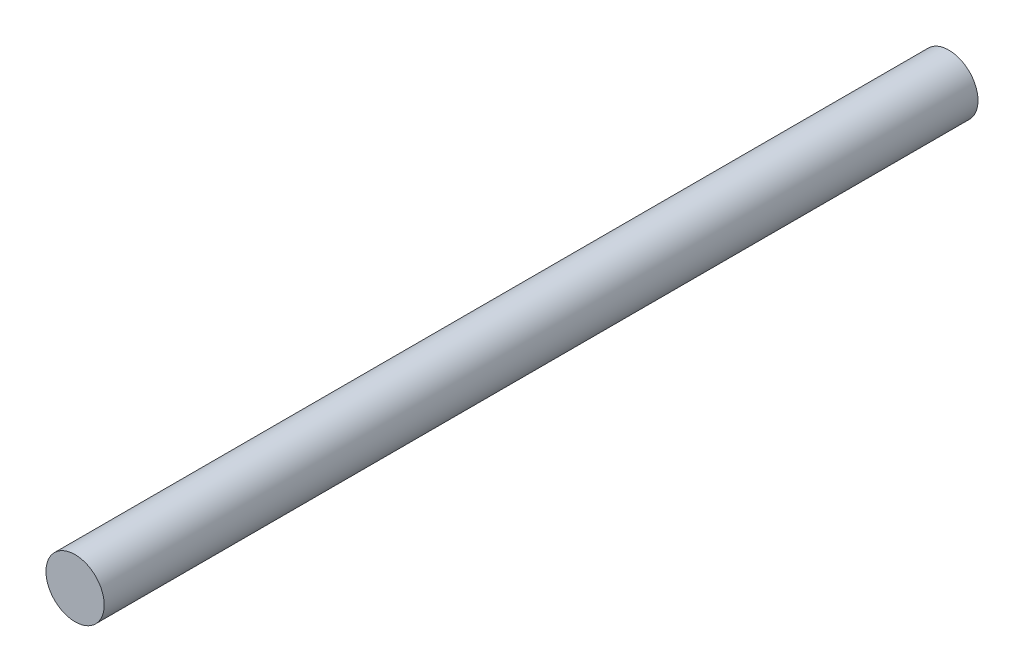
SolidWorks part; units mm, degrees
ref_plane "Plano frontal" through (0, 0, 0) normal (0, 0, 1) x (1, 0, 0)
ref_plane "Plano superior" through (0, 0, 0) normal (0, 1, 0) x (1, 0, 0)
ref_plane "Plano direito" through (0, 0, 0) normal (1, 0, 0) x (0, 0, -1)
sketch "Esboço1" plane through (0, 0, 0) normal (0, 0, 1) x (1, 0, 0)
  circle A0 centre (-4.2569, 1.5868) radius 5
  dimension "D1" = 10
extrude "Ressalto-extrusão1" add sketch "Esboço1" along normal blind 150
